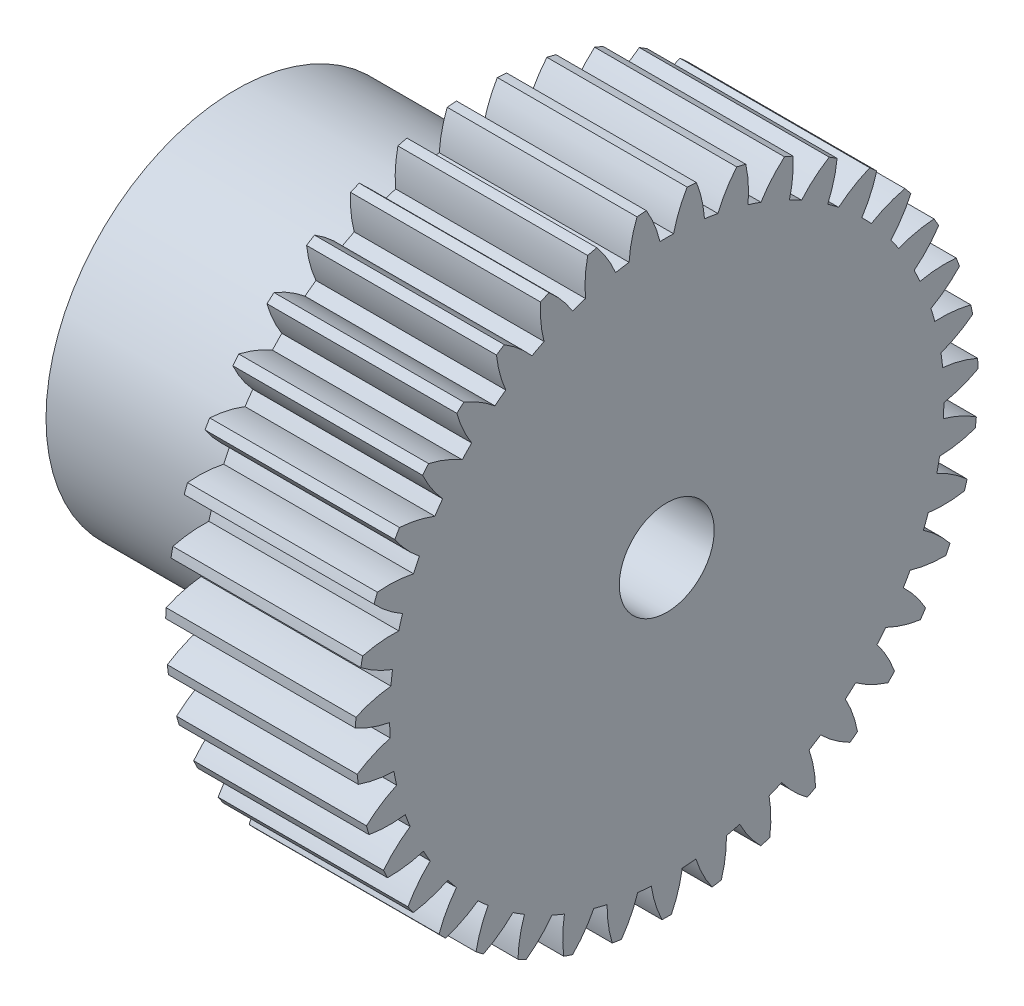
SolidWorks part; units mm, degrees
ref_plane "Plane1" through (0, 0, 0) normal (0, 0, 1) x (1, 0, 0)
ref_plane "Plane2" through (0, 0, 0) normal (0, 1, 0) x (1, 0, 0)
ref_plane "Plane3" through (0, 0, 0) normal (1, 0, 0) x (0, 0, -1)
sketch "HoldingSke" plane through (0, 0, 0) normal (0, 1, 0) x (1, 0, 0)
  line L0 (0, 0) -> (0.9714, -0.7867)
  line L1 (-15, 0) -> (100, 0) construction
  line L2 (0, 0) -> (-2.1039, 2.3779)
  line L3 (0, 0) -> (-11.863, 4.5341)
  line L4 (0, 0) -> (6.7114, 5.4348)
  line L5 (0, 0) -> (-9.3695, -3.4946)
  line L6 (0, 0) -> (-8.2896, -5.593)
  line L7 (-2.1039, 2.3779) -> (0.0486, 12.1435)
  line L8 (-76.2, 54.61) -> (-75.3, 54.61)
  line L9 (-71.009, 38.7566) -> (-53.1078, 45.2721)
  line L10 (-76.2, 71.12) -> (104.1128, 71.12)
  line L11 (0, 0) -> (-10, 0)
  line L12 (-76.2, 101.6) -> (-76.17, 101.6)
  line L13 (24.9733, 27.94) -> (52.9518, 28.4284)
  line L14 (24.9733, 27.94) -> (24.9743, 27.94)
  line L15 (24.9733, 27.94) -> (100.4006, 29.5858)
  line L16 (-63.627, -0.8) -> (-12.827, -0.8)
  circle A0 centre (0, 0) radius 2.5
  circle A1 centre (0, 0) radius 10
  circle A2 centre (0, 0) radius 10
  circle A3 centre (0, 0) radius 2.5
  dimension "MHD" = 20
  dimension "Hub_dia" = 20
  dimension "Bore" = 5
  dimension "MBD" = 5
  dimension "Num_teeth" = 39
  dimension "Pitch" = 1.25
  dimension "Overall_len" = 10
  dimension "Show_teeth" = 39
  dimension "Thickness" = 10
  dimension "OAL" = 10.0001
  dimension "T_dim" = 0.9
  dimension "Ap" = 20
  dimension "H" = 19.05
  dimension "Pitch_radius" = 180.3128
  dimension "Width" = 10
  dimension "Backlash" = 0.03
  dimension "Addendum_fac" = 1
  dimension "Dedendum_fac" = 1.25
  dimension "Clearance_fac" = 0.25
  dimension "Dedendum_add" = 0.001
  dimension "Module" = 0.8
sketch "BasProSke" plane through (0, 0, 0) normal (0, 1, 0) x (1, 0, 0)
  line L0 (-10, 0) -> (60, 0) construction
  line L1 (0, 0) -> (0, 16.4)
  line L2 (0, 0) -> (10, 0)
  line L3 (10, 0) -> (10, 16.4)
  line L4 (10, 16.4) -> (0, 16.4)
  dimension "Thickness" = 10
  dimension "Diameter" = 32.8
revolve "Base-Revolve" add sketch "BasProSke" angle 360 about L0
sketch "TooCutSke" plane through (0, 0, 0) normal (1, 0, 0) x (0, 0, -1)
  line L1 (0, 0) -> (0, 107) construction
  line L2 (0, 0) -> (-0.6806, 15.5851) construction
  line L3 (0, 0) -> (-2.5088, 31.0776) construction
  line L4 (-0.6806, 15.5851) -> (-1.2544, 15.5388) construction
  arc A0 (0.3593, 14.5946) -> (-0.3593, 14.5946) centre (0, 0) ccw
  arc A1 (1.0886, 16.3893) -> (-1.0886, 16.3893) centre (0, 0) ccw
  circle A2 centre (0, 0) radius 15.6 construction
  circle A3 centre (0, 0) radius 14.6592 construction
  arc A4 (-0.3593, 14.5946) -> (-1.0886, 16.3893) centre (-6.4349, 13.1714) ccw
  arc A5 (1.0886, 16.3893) -> (0.3593, 14.5946) centre (6.4349, 13.1714) ccw
  dimension "Root_dia" = 29.198
  dimension "Overcut_dia" = 32.8508
  dimension "Pitch_dia" = 31.2
  dimension "Base_dia" = 29.3184
  dimension "Flank_rad" = 6.24
  dimension "Half_ang" = 4.615
  dimension "Half_CT" = 0.5756
extrude "ToothCut" cut sketch "TooCutSke" along normal through all
fillet "Breaks" [suppressed] radius 0.016
fillet "RootFillets" [suppressed] radius 0.201
pattern_circular "TeethCuts" count 39 every 9.231 about axis through (-10, 0, 0) along (1, 0, 0) of "ToothCut", "RootFillets", "Breaks"
sketch "HubNeaOneSke" plane through (0, 0, 0) normal (-1, 0, 0) x (0, 0, 1)
  circle A0 centre (0, 0) radius 10
  dimension "Diameter" = 20
extrude "HubNearOne" add sketch "HubNeaOneSke" along normal blind 12.7001
sketch "HubNeaBotSke" plane through (0, 0, 0) normal (-1, 0, 0) x (0, 0, 1)
  circle A0 centre (0, 0) radius 10
  dimension "Diameter" = 20
extrude "HubNearBoth" [suppressed] add sketch "HubNeaBotSke" along normal blind 6.35
ref_plane "FarPln" through (10, 0, 0) normal (1, 0, 0) x (0, 0, -1)
sketch "HubFarSke" plane through (10, 0, 0) normal (1, 0, 0) x (0, 0, -1)
  circle A0 centre (0, 0) radius 10
  dimension "Diameter" = 20
extrude "HubFar" [suppressed] add sketch "HubFarSke" along normal blind 6.35
sketch "BorSke" plane through (0, 0, 0) normal (1, 0, 0) x (0, 0, -1)
  circle A0 centre (0, 0) radius 2.5
  dimension "Diameter" = 5
extrude "Bore" cut sketch "BorSke" along normal mid plane 20.0001
sketch "KeySke" plane through (0, 0, 0) normal (1, 0, 0) x (0, 0, -1)
  line L0 (-1, 0) -> (-1, 3.4)
  line L1 (-1, 3.4) -> (1, 3.4)
  line L2 (1, 3.4) -> (1, 0)
  line L3 (0, 0) -> (0, 34) construction
  line L4 (-1, 0) -> (1, 0)
  dimension "Offset" = 3.4
  dimension "Width" = 2
extrude "Keyway" [suppressed] cut sketch "KeySke" along normal mid plane 20.0001
pattern_circular "Keyway2" [suppressed] count 2 every 90 about axis through (-10, 0, 0) along (1, 0, 0)
equation "' \"Module@HoldingSke\" = 6.35"
equation "' \"Num_teeth@HoldingSke\" = 12"
equation "' \"Ap@HoldingSke\" =  20"
equation "' \"Ap@HoldingSke\" = 20"
equation "' \"Width@HoldingSke\" = 0.5 * 25.4"
equation "' \"Hub_dia@HoldingSke\"= 1 * 25.4"
equation "' \"Hub_dia@HoldingSke\" = 1 * 25.4"
equation "' \"Overall_len@HoldingSke\" = 1.0 * 25.4"
equation "' \"Bore@HoldingSke\" = 0.75 * 25.4"
equation "' \"T_dim@HoldingSke\" = 0.1 * 25.4"
equation "' \"Width@KeySke\" = 0.25 * 25.4"
equation "' \"Show_teeth@HoldingSke\" = 13"
equation "' \"Backlash@HoldingSke\" = 0.009 * 25.4"
equation "' \"Addendum_fac@HoldingSke\" = 1.0"
equation "' \"Dedendum_fac@HoldingSke\" = 1.25"
equation "' \"Dedendum_add@HoldingSke\" = 0.00005 * 25.4"
equation "' \"Clearance_fac@HoldingSke\" = 0.25"
equation "\"Pitch@HoldingSke\" = 1 / \"Module@HoldingSke\""
equation "\"Overcut_dia@TooCutSke\" = (\"Num_teeth@HoldingSke\" + 2 * \"Addendum_fac@HoldingSke\") / \"Pitch@HoldingSke\" + 0.002 * 25.4"
equation "\"Pitch_dia@TooCutSke\" = \"Num_teeth@HoldingSke\" / \"Pitch@HoldingSke\""
equation "\"Base_dia@TooCutSke\" = \"Num_teeth@HoldingSke\" / \"Pitch@HoldingSke\" * cos((\"Ap@HoldingSke\"  * 3.14159265 / 180))"
equation "\"Root_dia@TooCutSke\" = (\"Num_teeth@HoldingSke\" + 2) / \"Pitch@HoldingSke\" - 2 * (\"Addendum_fac@HoldingSke\" + \"Dedendum_fac@HoldingSke\") / \"Pitch@HoldingSke\" - \"Dedendum_add@HoldingSke\" * 2"
equation "\"Half_ang@TooCutSke\" = 180 / \"Num_teeth@HoldingSke\""
equation "\"Half_CT@TooCutSke\" = \"Num_teeth@HoldingSke\" / \"Pitch@HoldingSke\" * sin((3.14159265 / 2 / \"Num_teeth@HoldingSke\")) / 2 - 7 * \"Backlash@HoldingSke\" / 4"
equation "\"Flank_rad@TooCutSke\" = \"Num_teeth@HoldingSke\" / \"Pitch@HoldingSke\" / 5"
equation "\"Radius@RootFillets\" = \"Clearance_fac@HoldingSke\" / \"Pitch@HoldingSke\" + \"Dedendum_add@HoldingSke\""
equation "\"Break_rad@Breaks\" = 0.02 / \"Pitch@HoldingSke\""
equation "\"Thickness@HoldingSke\" = \"Width@HoldingSke\""
equation "\"OAL@HoldingSke\" = \"Thickness@HoldingSke\""
equation "\"MHD@HoldingSke\" = (\"Num_teeth@HoldingSke\" + 2) / \"Pitch@HoldingSke\" - 2 * (\"Addendum_fac@HoldingSke\" + \"Dedendum_fac@HoldingSke\")  / \"Pitch@HoldingSke\" - \"Dedendum_add@HoldingSke\" * 2"
equation "\"MBD@HoldingSke\" = (\"Num_teeth@HoldingSke\" + 2) / \"Pitch@HoldingSke\" - 2 * (\"Addendum_fac@HoldingSke\" + \"Dedendum_fac@HoldingSke\")  / \"Pitch@HoldingSke\" - \"Dedendum_add@HoldingSke\" * 2 - 0.002 * 25.4"
equation "\"MHD@HoldingSke\" = ((sgn( \"MHD@HoldingSke\" - \"Hub_dia@HoldingSke\" )-1)*( \"MHD@HoldingSke\" - \"Hub_dia@HoldingSke\" ))/-2+ \"Hub_dia@HoldingSke\""
equation "\"MBD@HoldingSke\" = ((sgn( \"MBD@HoldingSke\" - \"Bore@HoldingSke\" )-1)*( \"MBD@HoldingSke\" - \"Bore@HoldingSke\" ))/-2+ \"Bore@HoldingSke\""
equation "\"OAL@HoldingSke\" = ((sgn( \"OAL@HoldingSke\" - \"Overall_len@HoldingSke\" )+1)*( \"OAL@HoldingSke\" - \"Overall_len@HoldingSke\" ))/2 + \"Overall_len@HoldingSke\" + 0.000002 * 25.4"
equation "\"Num_teeth@TeethCuts\" = int( \"Show_teeth@HoldingSke\" ) + 1"
equation "\"Num_teeth@TeethCuts\" = ((sgn( \"Num_teeth@TeethCuts\" - \"Num_teeth@HoldingSke\" )-1)*( \"Num_teeth@TeethCuts\" - \"Num_teeth@HoldingSke\" ))/-2+ \"Num_teeth@HoldingSke\""
equation "\"Num_teeth@TeethCuts\" = ((sgn( \"Num_teeth@TeethCuts\" - 2.0)+1)*( \"Num_teeth@TeethCuts\" - 2.0))/2 +2.0"
equation "\"Angle@TeethCuts\" = 360.0 / \"Num_teeth@HoldingSke\""
equation "\"Diameter@BasProSke\" = (\"Num_teeth@HoldingSke\" + 2 * \"Addendum_fac@HoldingSke\") / \"Pitch@HoldingSke\""
equation "\"Thickness@BasProSke\"  = \"Thickness@HoldingSke\""
equation "' \"Fillet_rad@BasProSke\" =  \"Thickness@HoldingSke\" * 0.05"
equation "' \"Fillet_rad@BasProSke\" = \"Thickness@HoldingSke\" * 0.05"
equation "\"MHD@HoldingSke\" = ((sgn( \"MHD@HoldingSke\" - \"Root_dia@TooCutSke\" )-1)*( \"MHD@HoldingSke\" - \"Root_dia@TooCutSke\" ))/-2+ \"Root_dia@TooCutSke\""
equation "\"Diameter@HubNeaOneSke\" = \"MHD@HoldingSke\""
equation "\"Length@HubNearOne\" = \"OAL@HoldingSke\" - \"Thickness@BasProSke\""
equation "\"Diameter@HubNeaBotSke\" = \"MHD@HoldingSke\""
equation "\"Length@HubNearBoth\" = ( \"OAL@HoldingSke\" - \"Thickness@BasProSke\" ) / 2.0"
equation "\"Thickness@FarPln\" = \"Thickness@BasProSke\""
equation "\"Diameter@HubFarSke\" = \"MHD@HoldingSke\""
equation "\"Length@HubFar\" = ( \"OAL@HoldingSke\" - \"Thickness@BasProSke\" ) / 2.0"
equation "\"Diameter@BorSke\" = \"MBD@HoldingSke\""
equation "\"D1@Bore\" = \"OAL@HoldingSke\" * 2.0"
equation "\"D1@Keyway\" = \"OAL@HoldingSke\" * 2.0"
equation "\"Offset@KeySke\" = \"T_dim@HoldingSke\" + \"MBD@HoldingSke\" / 2.0"
